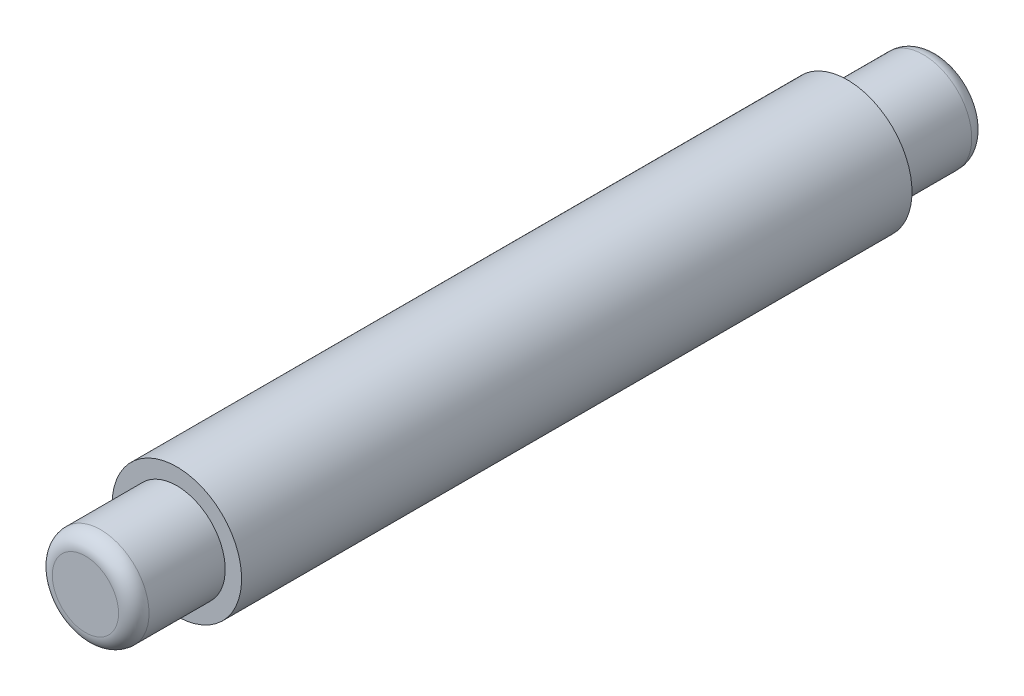
SolidWorks part; units mm, degrees
ref_plane "Front Plane" through (0, 0, 0) normal (0, 0, 1) x (1, 0, 0)
ref_plane "Top Plane" through (0, 0, 0) normal (0, 1, 0) x (1, 0, 0)
ref_plane "Right Plane" through (0, 0, 0) normal (1, 0, 0) x (0, 0, -1)
sketch "Sketch1" plane through (0, 0, 0) normal (0, 0, 1) x (1, 0, 0)
  circle A0 centre (0, 0) radius 3.175
  dimension "D1" = 6.35
extrude "Boss-Extrude1" add sketch "Sketch1" along normal blind 6
sketch "Sketch2" plane through (0, 0, 0) normal (0, 0, -1) x (-1, 0, 0)
  circle A0 centre (0, 0) radius 4.25
  dimension "D1" = 8.5
extrude "Boss-Extrude2" add sketch "Sketch2" along normal blind 44
sketch "Sketch3" plane through (0, 0, -44) normal (0, 0, -1) x (-1, 0, 0)
  circle A0 centre (0, 0) radius 3.175
  dimension "D1" = 6.35
extrude "Boss-Extrude3" add sketch "Sketch3" along normal blind 6
fillet "Fillet1" radius 1 2 edges at (-3.175, 0, -50) (3.175, 0, 6)
